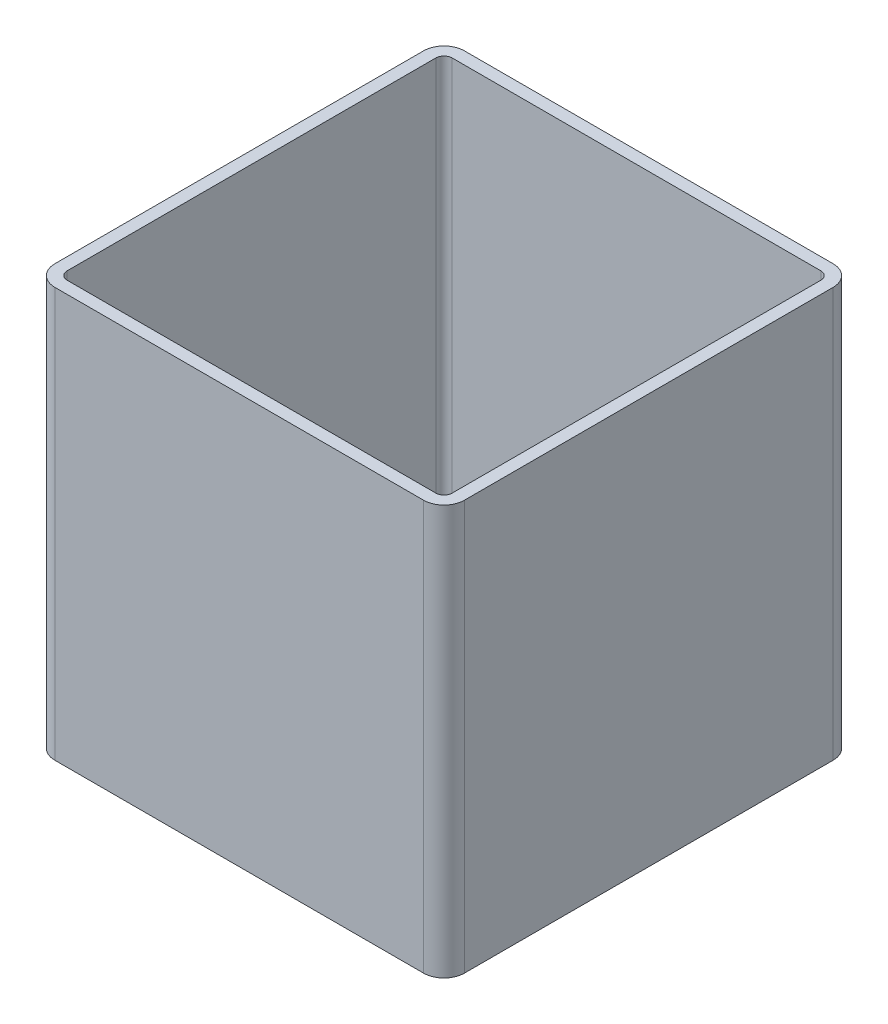
SolidWorks part; units mm, degrees
ref_plane "Спереди" through (0, 0, 0) normal (0, 0, 1) x (1, 0, 0)
ref_plane "Сверху" through (0, 0, 0) normal (0, 1, 0) x (1, 0, 0)
ref_plane "Справа" through (0, 0, 0) normal (1, 0, 0) x (0, 0, -1)
sketch "Эскиз1" plane through (0, 0, 0) normal (0, 1, 0) x (1, 0, 0)
  line L1 (-45, 50) -> (45, 50)
  line L2 (-50, 45) -> (-50, -45)
  line L3 (-45, -50) -> (45, -50)
  line L4 (50, 45) -> (50, -45)
  line L5 (-50, 50) -> (50, -50) construction
  line L6 (-50, -50) -> (50, 50) construction
  arc A0 (-50, -45) -> (-45, -50) centre (-45, -45) ccw
  arc A1 (45, -50) -> (50, -45) centre (45, -45) ccw
  arc A2 (45, 50) -> (50, 45) centre (45, 45) cw
  arc A3 (-45, 50) -> (-50, 45) centre (-45, 45) ccw
  point P0 (0, 0)
  dimension "D1" = 5
extrude "Вытянуть-Тонкостенный1" add sketch "Эскиз1" along normal blind 100 thin
